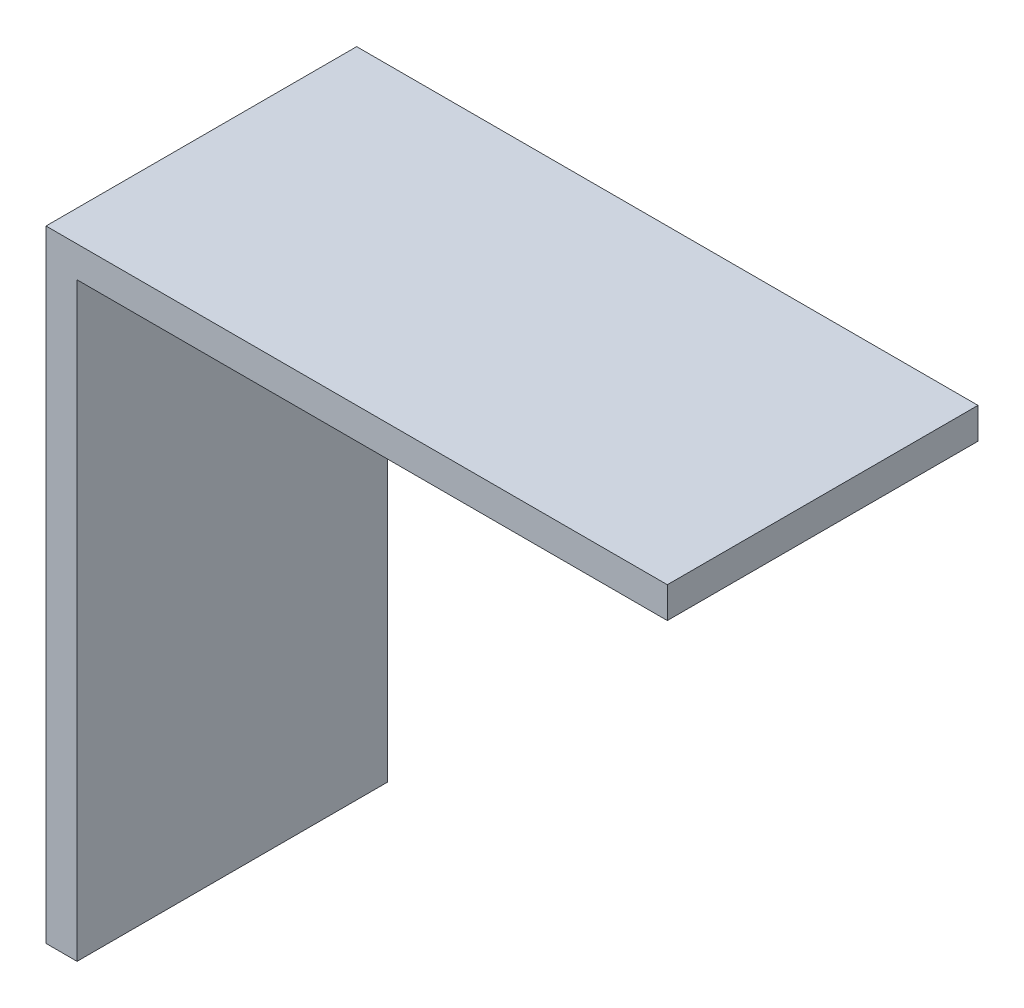
SolidWorks part; units mm, degrees
ref_plane "Front Plane" through (0, 0, 0) normal (0, 0, 1) x (1, 0, 0)
ref_plane "Top Plane" through (0, 0, 0) normal (0, 1, 0) x (1, 0, 0)
ref_plane "Right Plane" through (0, 0, 0) normal (1, 0, 0) x (0, 0, -1)
sketch "Sketch1" plane through (0, 0, 0) normal (0, 1, 0) x (1, 0, 0)
  line L1 (-20, 10) -> (20, 10)
  line L2 (-20, 10) -> (-20, -10)
  line L3 (-20, -10) -> (20, -10)
  line L4 (20, 10) -> (20, -10)
  line L5 (-20, 10) -> (20, -10) construction
  line L6 (-20, -10) -> (20, 10) construction
  point P0 (0, 0)
extrude "Boss-Extrude1" add sketch "Sketch1" along normal blind 2
sketch "Sketch2" plane through (0, 0, 0) normal (0, -1, 0) x (1, 0, 0)
  line L0 (20, -10) -> (-20, -10) construction
  line L1 (-20, 10) -> (-18, 10)
  line L2 (-20, 10) -> (-20, -10)
  line L3 (-20, -10) -> (-18, -10)
  line L4 (-18, 10) -> (-18, -10)
extrude "Boss-Extrude2" add sketch "Sketch2" along normal blind 38 contours L2 L1 L4 L3
